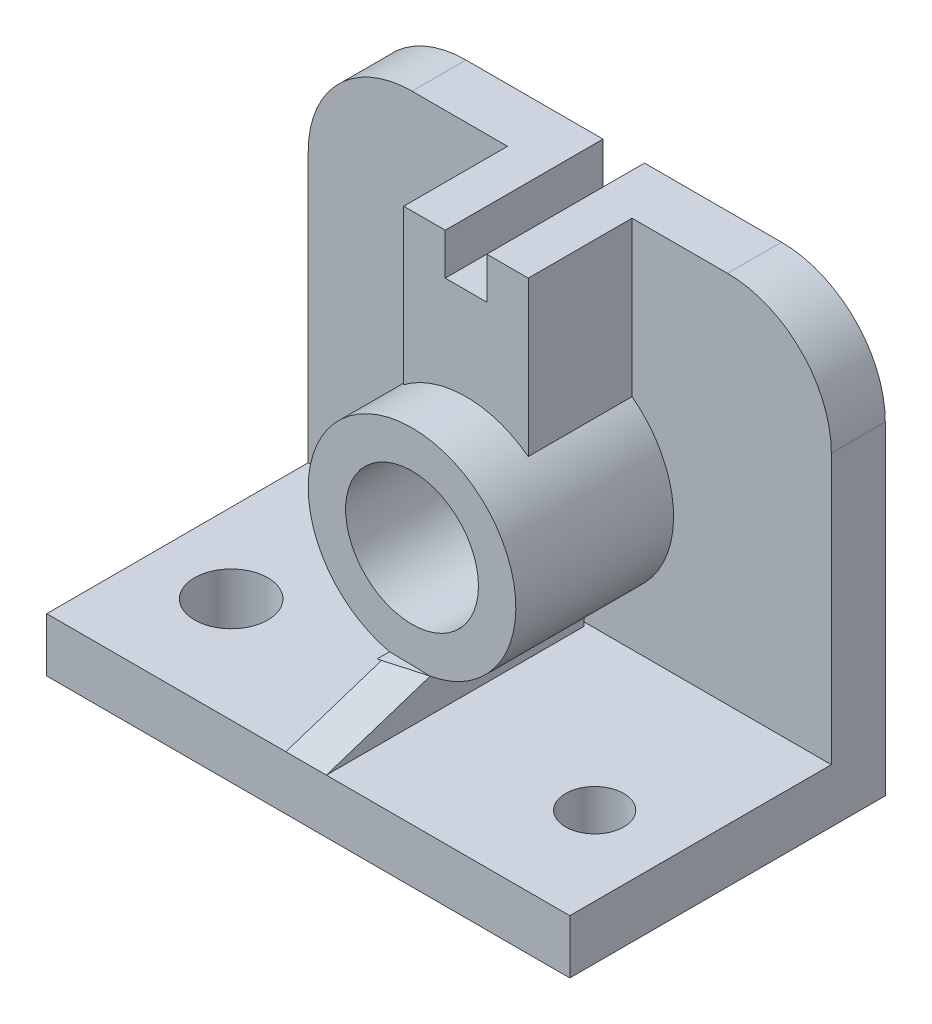
SolidWorks part; units mm, degrees
ref_plane "Front Plane" through (0, 0, 0) normal (0, 0, 1) x (1, 0, 0)
ref_plane "Top Plane" through (0, 0, 0) normal (0, 1, 0) x (1, 0, 0)
ref_plane "Right Plane" through (0, 0, 0) normal (1, 0, 0) x (0, 0, -1)
sketch "Sketch1" plane through (0, 0, 0) normal (0, 1, 0) x (1, 0, 0)
  line L1 (-53.9353, -0.5971) -> (72.0647, -0.5971)
  line L2 (-53.9353, -0.5971) -> (-53.9353, -76.5971)
  line L3 (-53.9353, -76.5971) -> (72.0647, -76.5971)
  line L4 (72.0647, -0.5971) -> (72.0647, -76.5971)
  dimension "D1" = 126
  dimension "D2" = 76
extrude "Boss-Extrude1" add sketch "Sketch1" along normal blind 13
sketch "Sketch2" plane through (0, 0, 0.5971) normal (0, 0, -1) x (-1, 0, 0)
  line L0 (-72.0647, 13) -> (-72.0647, 103)
  line L1 (53.9353, 13) -> (53.9353, 103)
  line L2 (-72.0647, 103) -> (53.9353, 103)
  line L3 (-72.0647, 13) -> (53.9353, 13)
  dimension "D1" = 90
  dimension "D2" = 90
extrude "Boss-Extrude2" add sketch "Sketch2" against normal blind 13
fillet "Fillet1" radius 25 2 edges at (72.0647, 103, 7.0971) (-53.9353, 103, 7.0971)
sketch "Sketch3" plane through (0, 103, 0) normal (0, 1, 0) x (1, 0, 0)
  line L0 (-53.9353, -0.5971) -> (72.0647, -0.5971) construction
  line L1 (9.0647, -0.5971) -> (9.0647, -13.5971) construction
  line L2 (72.0647, -13.5971) -> (-53.9353, -13.5971) construction
  line L3 (4.0647, -13.5971) -> (14.0647, -13.5971)
  line L4 (4.0647, -13.5971) -> (4.0647, -39.057)
  line L5 (14.0647, -13.5971) -> (14.0647, -39.057)
  line L6 (14.0647, -39.057) -> (4.0647, -39.057)
  point P11 (9.0647, -13.5971)
  dimension "D1" = 10
extrude "Boss-Extrude3" add sketch "Sketch3" against normal blind 10
sketch "Sketch4" plane through (0, 103, 0) normal (0, 1, 0) x (1, 0, 0)
  line L0 (4.0647, -13.5971) -> (4.0647, -0.5971) construction
  line L1 (-28.9353, -0.5971) -> (47.0647, -0.5971) construction
  line L3 (4.0647, -0.5971) -> (14.0647, -0.5971)
  line L4 (4.0647, -0.5971) -> (4.0647, -13.5971)
  line L5 (4.0647, -13.5971) -> (14.0647, -13.5971)
  line L6 (14.0647, -0.5971) -> (14.0647, -13.5971)
extrude "Cut-Extrude1" cut sketch "Sketch4" against normal blind 10
sketch "Sketch8" plane through (0, 0, 13.5971) normal (0, 0, 1) x (1, 0, 0)
  line L0 (-53.9353, 13) -> (72.0647, 13) construction
  circle A0 centre (9.0647, 45.7757) radius 25
  dimension "D1" = 50
extrude "Boss-Extrude4" add sketch "Sketch8" along normal blind 38
sketch "Sketch10" plane through (0, 0, 51.5971) normal (0, 0, 1) x (1, 0, 0)
  circle A0 centre (9.0647, 45.7757) radius 16
  dimension "D1" = 32
extrude "Cut-Extrude3" cut sketch "Sketch10" against normal blind 38
sketch "Sketch11" plane through (0, 0, 13.5971) normal (0, 0, 1) x (1, 0, 0)
  line L0 (4.0647, 103) -> (-5.9353, 103)
  line L1 (-28.9353, 103) -> (4.0647, 103) construction
  line L2 (-5.9353, 103) -> (-5.9353, 65.7757)
  line L3 (14.0647, 103) -> (24.0647, 103)
  line L4 (14.0647, 103) -> (47.0647, 103) construction
  line L5 (24.0647, 103) -> (24.0647, 65.7757)
  line L6 (14.0647, 103) -> (14.0647, 93)
  line L7 (14.0647, 93) -> (4.0647, 93)
  line L8 (4.0647, 93) -> (4.0647, 103)
  circle A0 centre (9.0647, 45.7757) radius 25 construction
  arc A1 (24.0647, 65.7757) -> (-5.9353, 65.7757) centre (9.0647, 45.7757) ccw
  dimension "D1" = 10
  dimension "D2" = 10
extrude "Boss-Extrude8" add sketch "Sketch11" along normal blind 25
sketch "Sketch12" plane through (0, 0, 39.057) normal (0, 0, 1) x (1, 0, 0)
  line L1 (4.0647, 103) -> (14.0647, 103)
  line L2 (4.0647, 103) -> (4.0647, 93)
  line L3 (4.0647, 93) -> (14.0647, 93)
  line L4 (14.0647, 103) -> (14.0647, 93)
extrude "Cut-Extrude4" cut sketch "Sketch12" against normal blind 45
sketch "Sketch13" plane through (0, 13, 0) normal (0, 1, 0) x (1, 0, 0)
  line L0 (-53.9353, -76.5971) -> (-53.9353, -51.2901) construction
  line L1 (-53.9353, -13.5971) -> (-53.9353, -76.5971) construction
  line L2 (-53.9353, -51.2901) -> (-34.8089, -51.2901) construction
  circle A0 centre (-34.8089, -51.2901) radius 8.8299
extrude "Cut-Extrude5" cut sketch "Sketch13" against normal blind 14
sketch "Sketch14" plane through (0, 13, 0) normal (0, 1, 0) x (1, 0, 0)
  line L0 (72.0647, -76.5971) -> (72.0647, -51.5971) construction
  line L1 (72.0647, -76.5971) -> (72.0647, -13.5971) construction
  line L2 (72.0647, -51.5971) -> (53.0647, -51.5971) construction
  circle A0 centre (53.0647, -51.5971) radius 7
  dimension "D3" = 14
  dimension "D1" = 25
  dimension "D2" = 19
extrude "Cut-Extrude6" cut sketch "Sketch14" against normal blind 34
sketch "Sketch17" plane through (0, 0, 51.5971) normal (0, 0, 1) x (1, 0, 0)
  line L0 (3.6604, 21.3668) -> (13.4311, 21.1599)
  line L1 (13.4311, 21.1599) -> (13.4311, 13)
  line L2 (72.0647, 13) -> (-53.9353, 13) construction
  line L3 (13.4311, 13) -> (3.6604, 13)
  line L4 (-53.9353, 13) -> (72.0647, 13) construction
  line L5 (3.6604, 13) -> (3.6604, 21.3668)
  arc A0 (-5.9353, 65.7757) -> (24.0647, 65.7757) centre (9.0647, 45.7757) ccw construction
extrude "Boss-Extrude11" add sketch "Sketch17" along normal mid plane 74
sketch "Sketch18" plane through (13.4311, 0, 0) normal (1, 0, 0) x (0, 0, -1)
  line L0 (-51.5971, 21.1599) -> (-76.5971, 13)
  line L1 (-76.5971, 13) -> (-88.5971, 13)
  line L2 (-88.5971, 13) -> (-88.5971, 21.1599) construction
  line L3 (-88.5971, 13) -> (-76.5971, 13) construction
  line L4 (-88.5971, 13) -> (-88.5971, 23.6839)
  line L6 (-88.5971, 23.6839) -> (-51.5971, 21.1599)
extrude "Cut-Extrude7" cut sketch "Sketch18" against normal mid plane 74
